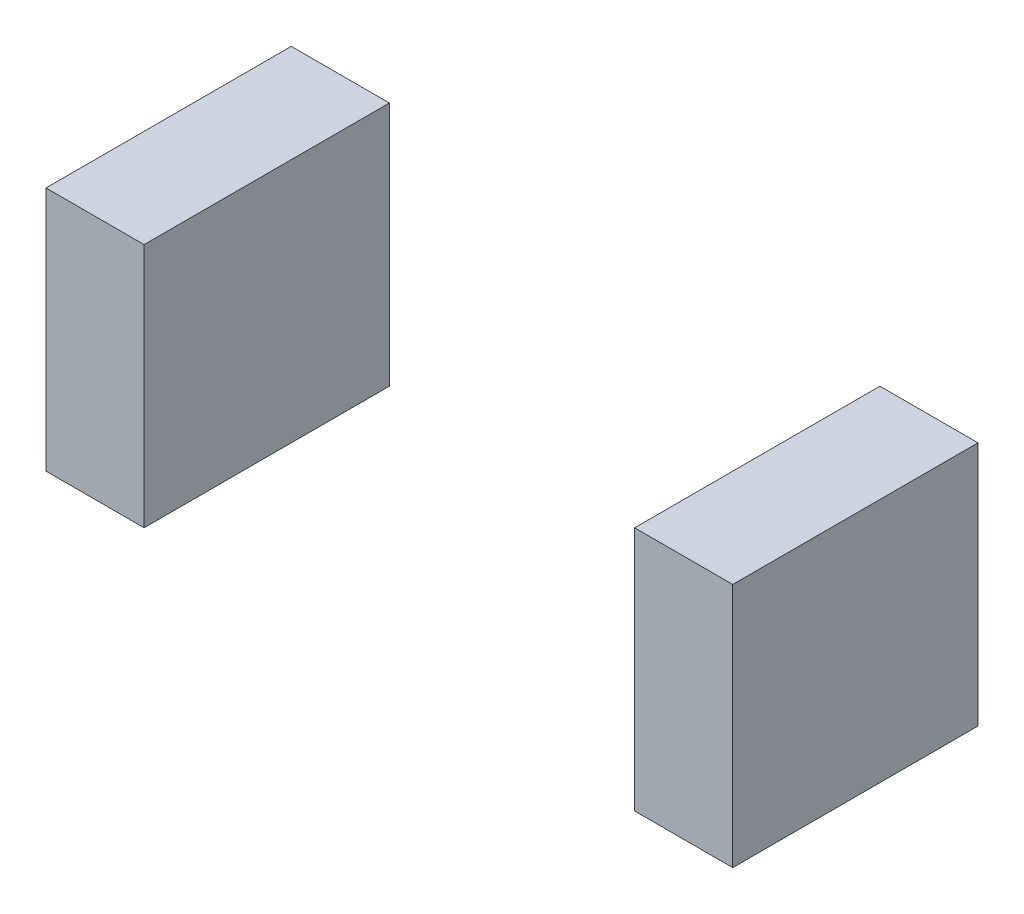
SolidWorks part; units mm, degrees
ref_plane "Płaszczyzna przednia" through (0, 0, 0) normal (0, 0, 1) x (1, 0, 0)
ref_plane "Płaszczyzna górna" through (0, 0, 0) normal (0, 1, 0) x (1, 0, 0)
ref_plane "Płaszczyzna prawa" through (0, 0, 0) normal (1, 0, 0) x (0, 0, -1)
sketch "Szkic1" plane through (0, 0, 0) normal (0, 0, 1) x (1, 0, 0)
  line L1 (0, 0) -> (20, 0)
  line L2 (0, 0) -> (0, 50)
  line L3 (0, 50) -> (20, 50)
  line L4 (20, 0) -> (20, 50)
  dimension "D1" = 20
  dimension "D2" = 50
extrude "Dodanie-wyciągnięcie1" add sketch "Szkic1" along normal blind 50
pattern_linear "Szyk liniowy1" count 2 spacing 120 along (1, 0, 0) of "Dodanie-wyciągnięcie1"
